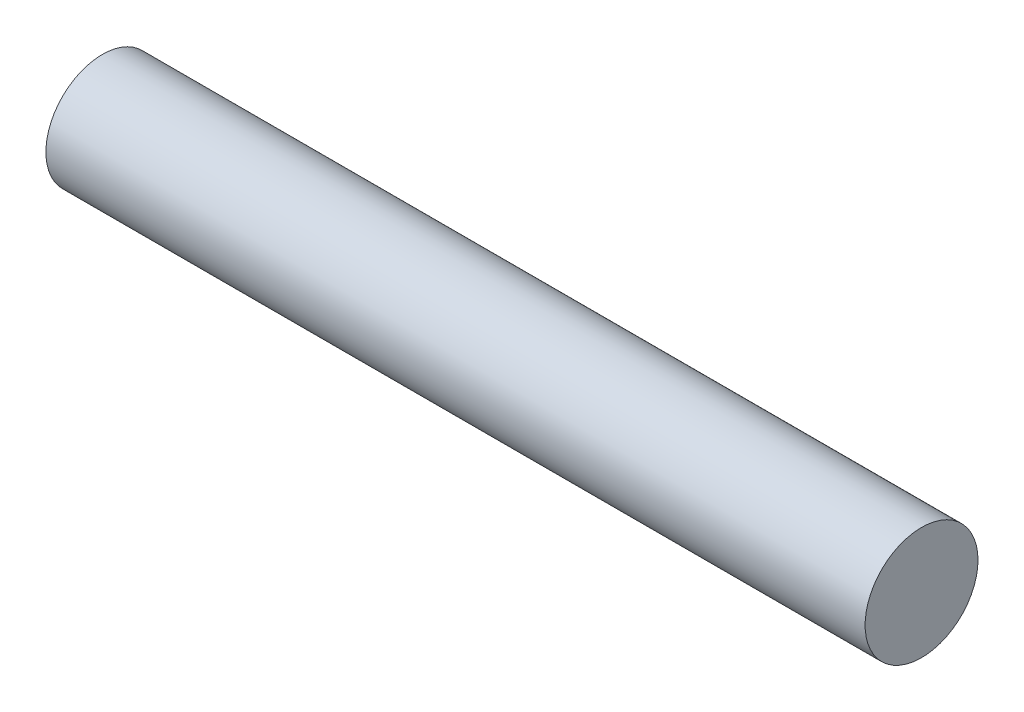
SolidWorks part; units mm, degrees
ref_plane "Front Plane" through (0, 0, 0) normal (0, 0, 1) x (1, 0, 0)
ref_plane "Top Plane" through (0, 0, 0) normal (0, 1, 0) x (1, 0, 0)
ref_plane "Right Plane" through (0, 0, 0) normal (1, 0, 0) x (0, 0, -1)
sketch "Sketch1" plane through (0, 0, 0) normal (1, 0, 0) x (0, 0, -1)
  circle A0 centre (0, 0) radius 0.175
  dimension "D1" = 0.35
extrude "Boss-Extrude1" add sketch "Sketch1" along normal blind 2.54 contours A0
